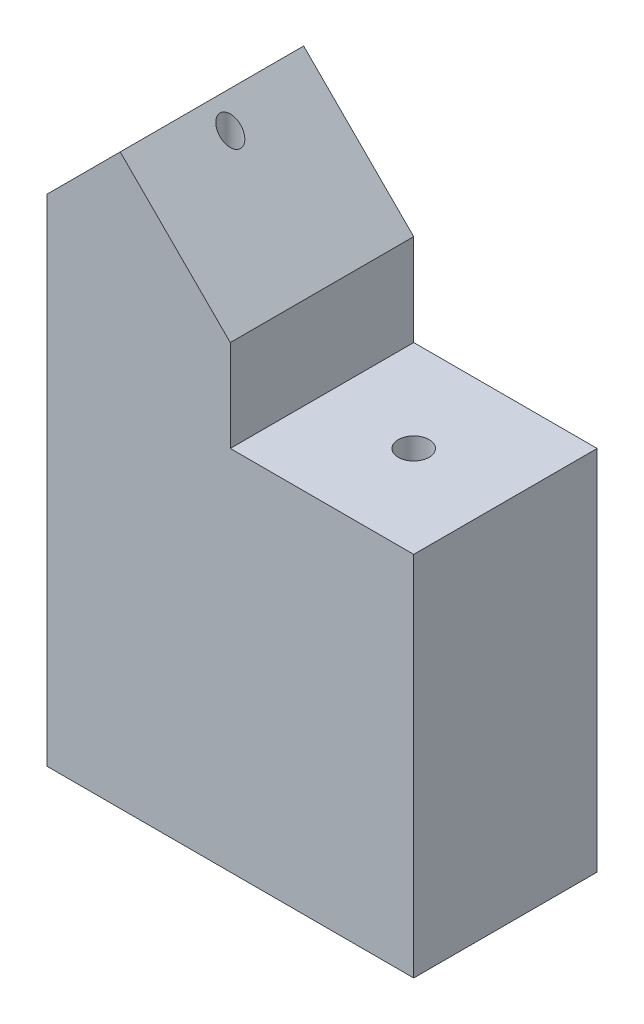
SolidWorks part; units mm, degrees
ref_plane "Front" through (0, 0, 0) normal (0, 0, 1) x (1, 0, 0)
ref_plane "Top" through (0, 0, 0) normal (0, 1, 0) x (1, 0, 0)
ref_plane "Right" through (0, 0, 0) normal (1, 0, 0) x (0, 0, -1)
sketch "Sketch1" plane through (0, 0, 0) normal (0, 1, 0) x (1, 0, 0)
  line L1 (5, 2.5) -> (-5, 2.5)
  line L2 (5, 2.5) -> (5, -2.5)
  line L3 (5, -2.5) -> (-5, -2.5)
  line L4 (-5, 2.5) -> (-5, -2.5)
  line L5 (5, 2.5) -> (-5, -2.5) construction
  line L6 (5, -2.5) -> (-5, 2.5) construction
  point P0 (0, 0)
  dimension "D1" = 10
  dimension "D2" = 5
extrude "Boss-Extrude1" add sketch "Sketch1" along normal blind 20
sketch "Sketch2" plane through (0, 0, 0) normal (0, -1, 0) x (1, 0, 0)
  line L1 (5, 2.5) -> (5, -2.5) construction
  line L2 (0, 0) -> (-5, 0) construction
  line L3 (-5, -2.5) -> (-5, 2.5) construction
  line L5 (0, 0) -> (5, 0) construction
  circle A0 centre (2.5, 0) radius 0.42
  circle A1 centre (-2.5, 0) radius 0.28
  point P11 (0, 0)
  point P13 (0, 0)
  dimension "D1" = 0.84
  dimension "D2" = 0.56
extrude "Cut-Extrude1" cut sketch "Sketch2" against normal through all
sketch "Sketch3" plane through (0, 0, 0) normal (0, 0, 1) x (1, 0, 0)
  line L0 (-5, 17.5) -> (0, 12.5)
  line L1 (-5, 20) -> (-5, 0) construction
  line L3 (5, 20) -> (5, 0) construction
  line L4 (5, 10) -> (5, 20)
  line L5 (5, 20) -> (-5, 20)
  line L6 (-5, 20) -> (-5, 17.5)
  line L9 (-5, 0) -> (5, 0) construction
  line L10 (-2.5, 15) -> (-2.5, 0) construction
  line L11 (2.5, 0) -> (2.5, 10) construction
  line L12 (-2.78, 0) -> (-2.22, 0) construction
  line L13 (2.08, 0) -> (2.92, 0) construction
  line L14 (0, 12.5) -> (0, 10)
  line L15 (0, 10) -> (5, 10)
  point P13 (0, 0)
  dimension "D1" = 45
  dimension "D2" = 15
  dimension "D3" = 10
extrude "Cut-Extrude2" cut sketch "Sketch3" against normal through all both and the other way through all
chamfer "Chamfer1" distance 4 angle 45 1 edges at (-5, 17.5, 0)
